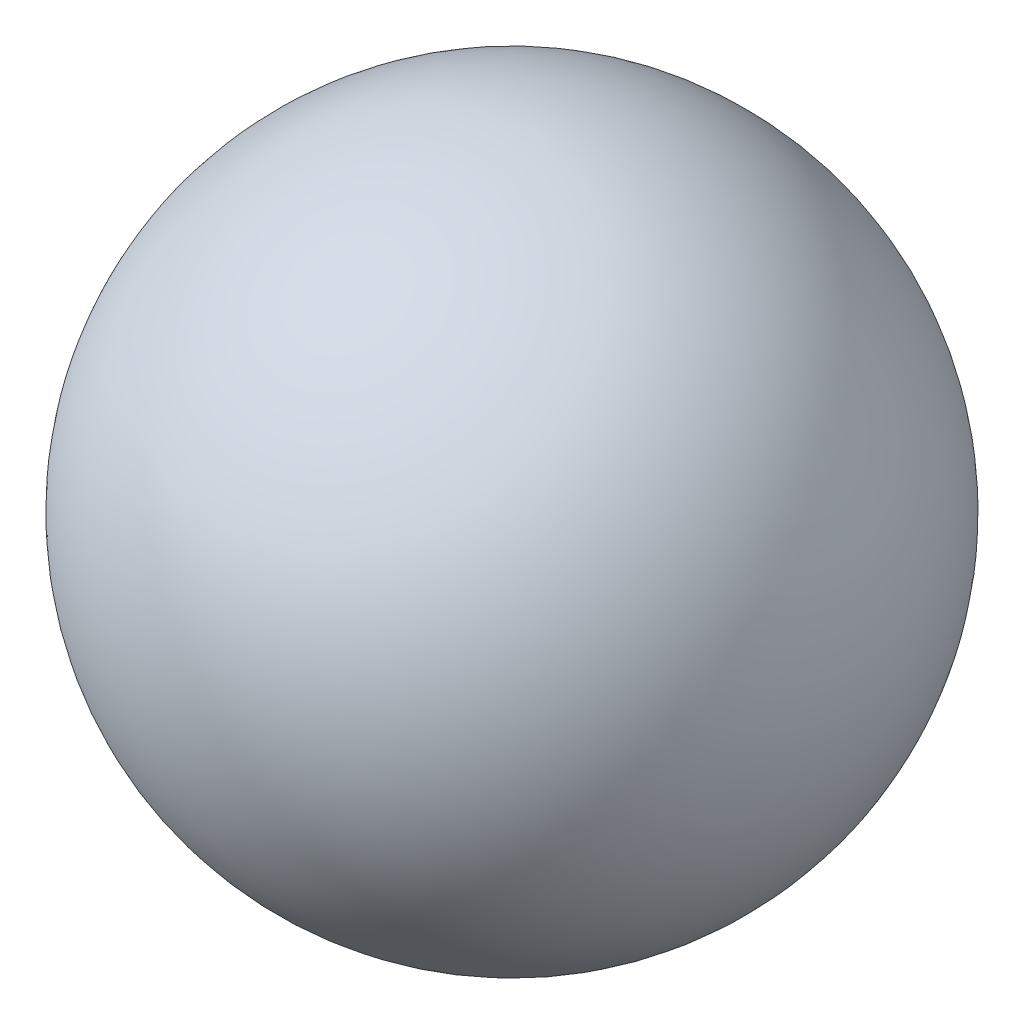
SolidWorks part; units mm, degrees
ref_plane "Front Plane" through (0, 0, 0) normal (0, 0, 1) x (1, 0, 0)
ref_plane "Top Plane" through (0, 0, 0) normal (0, 1, 0) x (1, 0, 0)
ref_plane "Right Plane" through (0, 0, 0) normal (1, 0, 0) x (0, 0, -1)
sketch "Sketch2" plane through (0, 0, 0) normal (0, 0, 1) x (1, 0, 0)
  line L0 (-88.9, 0) -> (88.9, 0)
  arc A1 (88.9, 0) -> (-88.9, 0) centre (0, 0) ccw
  point P5 (0, 0)
  dimension "D1" = 177.8
revolve "Revolve1" add sketch "Sketch2" angle 360 about L0
